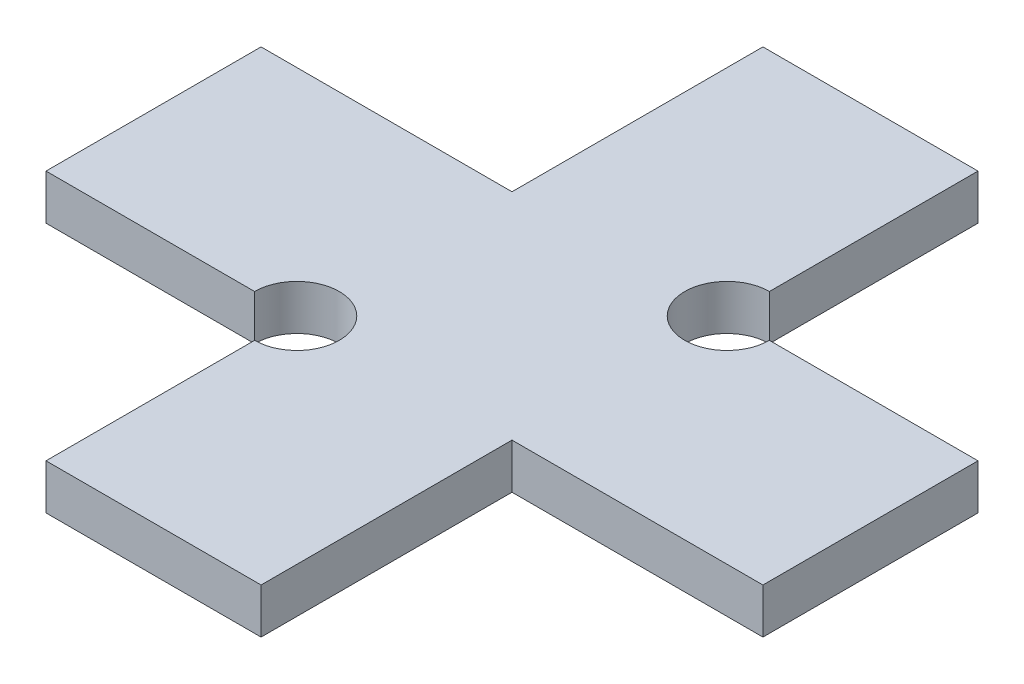
SolidWorks part; units mm, degrees
ref_plane "Front Plane" through (0, 0, 0) normal (0, 0, 1) x (1, 0, 0)
ref_plane "Top Plane" through (0, 0, 0) normal (0, 1, 0) x (1, 0, 0)
ref_plane "Right Plane" through (0, 0, 0) normal (1, 0, 0) x (0, 0, -1)
sketch "Sketch1" plane through (0, 0, 0) normal (0, 1, 0) x (1, 0, 0)
  line L1 (3.81, -12.7) -> (-3.81, -12.7)
  line L2 (3.81, -12.7) -> (3.81, 12.7)
  line L3 (3.81, 12.7) -> (-3.81, 12.7)
  line L4 (-3.81, -12.7) -> (-3.81, 12.7)
  line L5 (3.81, -12.7) -> (-3.81, 12.7) construction
  line L6 (3.81, 12.7) -> (-3.81, -12.7) construction
  line L7 (12.7, -3.81) -> (-12.7, -3.81)
  line L8 (12.7, -3.81) -> (12.7, 3.81)
  line L9 (12.7, 3.81) -> (-12.7, 3.81)
  line L10 (-12.7, -3.81) -> (-12.7, 3.81)
  line L11 (12.7, -3.81) -> (-12.7, 3.81) construction
  line L12 (12.7, 3.81) -> (-12.7, -3.81) construction
  circle A0 centre (3.81, 3.81) radius 1.5
  circle A1 centre (-3.81, -3.81) radius 1.5
  point P0 (0, 0)
  point P6 (0, 0)
  dimension "D5" = 3
  dimension "D6" = 3
  dimension "D1" = 25.4
  dimension "D2" = 7.62
  dimension "D3" = 7.62
  dimension "D4" = 25.4
extrude "Boss-Extrude1" add sketch "Sketch1" along normal blind 1.6 contours A1 L4 L9 L10 L7 | A1 L7 L2 A0 L9 L4 | A1 L4 L1 L2 L7 | A0 L2 L7 L8 L9 | A0 L2 L3 L4 L9
